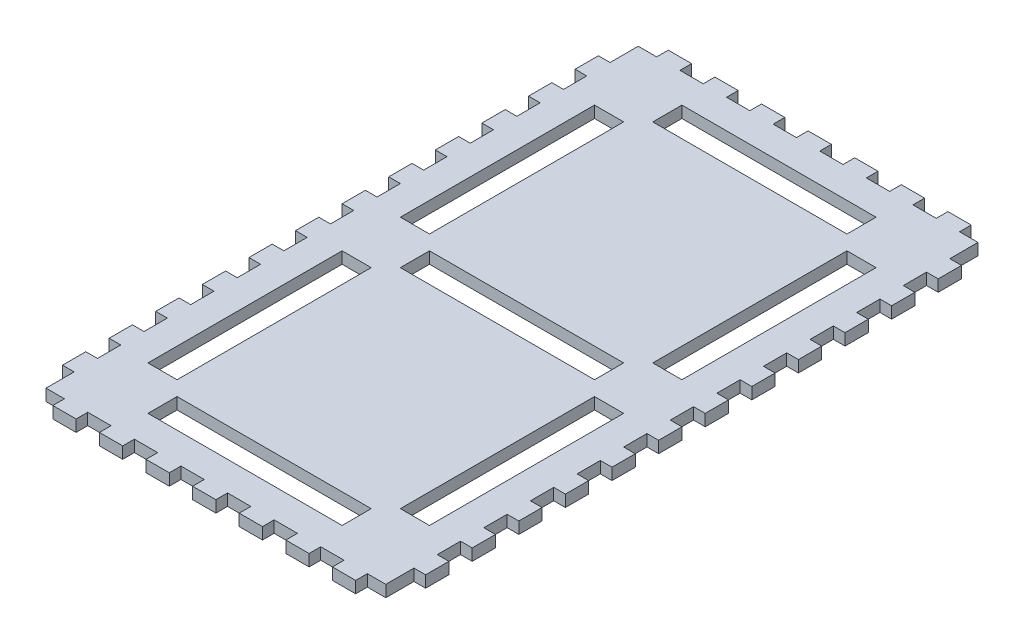
SolidWorks part; units mm, degrees
ref_plane "Front Plane" through (0, 0, 0) normal (0, 0, 1) x (1, 0, 0)
ref_plane "Top Plane" through (0, 0, 0) normal (0, 1, 0) x (1, 0, 0)
ref_plane "Right Plane" through (0, 0, 0) normal (1, 0, 0) x (0, 0, -1)
sketch "Sketch3" plane through (0, 0, 0) normal (0, 1, 0) x (1, 0, 0)
  line L1 (-87.5, -152.5) -> (87.5, -152.5)
  line L2 (-87.5, -152.5) -> (-87.5, 152.5)
  line L3 (-87.5, 152.5) -> (87.5, 152.5)
  line L4 (87.5, -152.5) -> (87.5, 152.5)
  line L5 (-87.5, -152.5) -> (87.5, 152.5) construction
  line L6 (-87.5, 152.5) -> (87.5, -152.5) construction
  line L7 (-50, 137.5) -> (50, 137.5)
  line L8 (-50, 137.5) -> (-50, 122.5)
  line L9 (-50, 122.5) -> (50, 122.5)
  line L10 (50, 137.5) -> (50, 122.5)
  line L22 (-72.5, 115) -> (-57.5, 115)
  line L23 (-72.5, 115) -> (-72.5, 15)
  line L24 (-72.5, 15) -> (-57.5, 15)
  line L25 (-57.5, 115) -> (-57.5, 15)
  line L26 (-50, -122.5) -> (50, -122.5)
  line L27 (-50, -122.5) -> (-50, -137.5)
  line L28 (-50, -137.5) -> (50, -137.5)
  line L29 (50, -122.5) -> (50, -137.5)
  line L34 (-50, 7.5) -> (50, 7.5)
  line L35 (-50, 7.5) -> (-50, -7.5)
  line L36 (-50, -7.5) -> (50, -7.5)
  line L37 (50, 7.5) -> (50, -7.5)
  line L42 (57.5, 115) -> (72.5, 115)
  line L43 (57.5, 115) -> (57.5, 15)
  line L44 (57.5, 15) -> (72.5, 15)
  line L45 (72.5, 115) -> (72.5, 15)
  line L46 (57.5, -15) -> (72.5, -15)
  line L47 (57.5, -15) -> (57.5, -115)
  line L48 (57.5, -115) -> (72.5, -115)
  line L49 (72.5, -15) -> (72.5, -115)
  line L50 (-72.5, -15) -> (-57.5, -15)
  line L51 (-72.5, -15) -> (-72.5, -115)
  line L52 (-72.5, -115) -> (-57.5, -115)
  line L53 (-57.5, -15) -> (-57.5, -115)
  line L74 (-54, 152.5) -> (-54, 158.5)
  line L79 (-78, 152.5) -> (-66, 152.5)
  line L80 (-78, 152.5) -> (-78, 158.5)
  line L81 (-78, 158.5) -> (-66, 158.5)
  line L82 (-66, 152.5) -> (-66, 158.5)
  line L83 (-54, 152.5) -> (-42, 152.5)
  line L84 (-42, 152.5) -> (-42, 158.5)
  line L85 (-54, 158.5) -> (-42, 158.5)
  line L86 (-30, 152.5) -> (-30, 158.5)
  line L87 (-30, 152.5) -> (-18, 152.5)
  line L88 (-18, 152.5) -> (-18, 158.5)
  line L89 (-30, 158.5) -> (-18, 158.5)
  line L90 (-6, 152.5) -> (-6, 158.5)
  line L91 (-6, 152.5) -> (6, 152.5)
  line L92 (6, 152.5) -> (6, 158.5)
  line L93 (-6, 158.5) -> (6, 158.5)
  line L94 (18, 152.5) -> (18, 158.5)
  line L95 (18, 152.5) -> (30, 152.5)
  line L96 (30, 152.5) -> (30, 158.5)
  line L97 (18, 158.5) -> (30, 158.5)
  line L98 (42, 152.5) -> (42, 158.5)
  line L99 (42, 152.5) -> (54, 152.5)
  line L100 (54, 152.5) -> (54, 158.5)
  line L101 (42, 158.5) -> (54, 158.5)
  line L102 (66, 152.5) -> (66, 158.5)
  line L103 (66, 152.5) -> (78, 152.5)
  line L104 (78, 152.5) -> (78, 158.5)
  line L105 (66, 158.5) -> (78, 158.5)
  line L106 (-87.5, 114) -> (-87.5, 102)
  line L107 (-87.5, 138) -> (-93.5, 138)
  line L108 (-87.5, 138) -> (-87.5, 126)
  line L109 (-87.5, 126) -> (-93.5, 126)
  line L110 (-93.5, 138) -> (-93.5, 126)
  line L111 (-87.5, 114) -> (-93.5, 114)
  line L112 (-93.5, 114) -> (-93.5, 102)
  line L113 (-87.5, 102) -> (-93.5, 102)
  line L114 (-87.5, 90) -> (-87.5, 78)
  line L115 (-87.5, 90) -> (-93.5, 90)
  line L116 (-93.5, 90) -> (-93.5, 78)
  line L117 (-87.5, 78) -> (-93.5, 78)
  line L118 (-87.5, 66) -> (-87.5, 54)
  line L119 (-87.5, 66) -> (-93.5, 66)
  line L120 (-93.5, 66) -> (-93.5, 54)
  line L121 (-87.5, 54) -> (-93.5, 54)
  line L122 (-87.5, 42) -> (-87.5, 30)
  line L123 (-87.5, 42) -> (-93.5, 42)
  line L124 (-93.5, 42) -> (-93.5, 30)
  line L125 (-87.5, 30) -> (-93.5, 30)
  line L126 (-87.5, 18) -> (-87.5, 6)
  line L127 (-87.5, 18) -> (-93.5, 18)
  line L128 (-93.5, 18) -> (-93.5, 6)
  line L129 (-87.5, 6) -> (-93.5, 6)
  line L130 (-87.5, -6) -> (-87.5, -18)
  line L131 (-87.5, -6) -> (-93.5, -6)
  line L132 (-93.5, -6) -> (-93.5, -18)
  line L133 (-87.5, -18) -> (-93.5, -18)
  line L134 (-87.5, -30) -> (-87.5, -42)
  line L135 (-87.5, -30) -> (-93.5, -30)
  line L136 (-93.5, -30) -> (-93.5, -42)
  line L137 (-87.5, -42) -> (-93.5, -42)
  line L138 (-87.5, -54) -> (-87.5, -66)
  line L139 (-87.5, -54) -> (-93.5, -54)
  line L140 (-93.5, -54) -> (-93.5, -66)
  line L141 (-87.5, -66) -> (-93.5, -66)
  line L142 (-87.5, -78) -> (-87.5, -90)
  line L143 (-87.5, -78) -> (-93.5, -78)
  line L144 (-93.5, -78) -> (-93.5, -90)
  line L145 (-87.5, -90) -> (-93.5, -90)
  line L146 (-87.5, -102) -> (-87.5, -114)
  line L147 (-87.5, -102) -> (-93.5, -102)
  line L148 (-93.5, -102) -> (-93.5, -114)
  line L149 (-87.5, -114) -> (-93.5, -114)
  line L150 (-87.5, -126) -> (-87.5, -138)
  line L151 (-87.5, -126) -> (-93.5, -126)
  line L152 (-93.5, -126) -> (-93.5, -138)
  line L153 (-87.5, -138) -> (-93.5, -138)
  line L154 (93.5, 114) -> (93.5, 102)
  line L155 (93.5, 102) -> (87.5, 102)
  line L156 (87.5, 114) -> (87.5, 102)
  line L157 (93.5, 114) -> (87.5, 114)
  line L158 (93.5, 138) -> (93.5, 126)
  line L159 (93.5, 138) -> (87.5, 138)
  line L160 (87.5, 138) -> (87.5, 126)
  line L161 (93.5, 126) -> (87.5, 126)
  line L162 (93.5, 90) -> (93.5, 78)
  line L163 (93.5, 78) -> (87.5, 78)
  line L164 (87.5, 90) -> (87.5, 78)
  line L165 (93.5, 90) -> (87.5, 90)
  line L166 (93.5, 66) -> (93.5, 54)
  line L167 (93.5, 54) -> (87.5, 54)
  line L168 (87.5, 66) -> (87.5, 54)
  line L169 (93.5, 66) -> (87.5, 66)
  line L170 (93.5, 42) -> (93.5, 30)
  line L171 (93.5, 30) -> (87.5, 30)
  line L172 (87.5, 42) -> (87.5, 30)
  line L173 (93.5, 42) -> (87.5, 42)
  line L174 (93.5, 18) -> (93.5, 6)
  line L175 (93.5, 6) -> (87.5, 6)
  line L176 (87.5, 18) -> (87.5, 6)
  line L177 (93.5, 18) -> (87.5, 18)
  line L178 (93.5, -6) -> (93.5, -18)
  line L179 (93.5, -18) -> (87.5, -18)
  line L180 (87.5, -6) -> (87.5, -18)
  line L181 (93.5, -6) -> (87.5, -6)
  line L182 (93.5, -30) -> (93.5, -42)
  line L183 (93.5, -42) -> (87.5, -42)
  line L184 (87.5, -30) -> (87.5, -42)
  line L185 (93.5, -30) -> (87.5, -30)
  line L186 (93.5, -54) -> (93.5, -66)
  line L187 (93.5, -66) -> (87.5, -66)
  line L188 (87.5, -54) -> (87.5, -66)
  line L189 (93.5, -54) -> (87.5, -54)
  line L190 (93.5, -78) -> (93.5, -90)
  line L191 (93.5, -90) -> (87.5, -90)
  line L192 (87.5, -78) -> (87.5, -90)
  line L193 (93.5, -78) -> (87.5, -78)
  line L194 (93.5, -102) -> (93.5, -114)
  line L195 (93.5, -114) -> (87.5, -114)
  line L196 (87.5, -102) -> (87.5, -114)
  line L197 (93.5, -102) -> (87.5, -102)
  line L198 (93.5, -126) -> (93.5, -138)
  line L199 (93.5, -138) -> (87.5, -138)
  line L200 (87.5, -126) -> (87.5, -138)
  line L201 (93.5, -126) -> (87.5, -126)
  line L202 (-87.5, 114) -> (93.5, 114) construction
  line L203 (66, -158.5) -> (66, -152.5)
  line L204 (66, -152.5) -> (78, -152.5)
  line L205 (78, -158.5) -> (78, -152.5)
  line L206 (66, -158.5) -> (78, -158.5)
  line L207 (42, -158.5) -> (42, -152.5)
  line L208 (42, -152.5) -> (54, -152.5)
  line L209 (54, -158.5) -> (54, -152.5)
  line L210 (42, -158.5) -> (54, -158.5)
  line L211 (18, -158.5) -> (18, -152.5)
  line L212 (18, -152.5) -> (30, -152.5)
  line L213 (30, -158.5) -> (30, -152.5)
  line L214 (18, -158.5) -> (30, -158.5)
  line L215 (-6, -158.5) -> (-6, -152.5)
  line L216 (-6, -152.5) -> (6, -152.5)
  line L217 (6, -158.5) -> (6, -152.5)
  line L218 (-6, -158.5) -> (6, -158.5)
  line L219 (-30, -158.5) -> (-30, -152.5)
  line L220 (-30, -152.5) -> (-18, -152.5)
  line L221 (-18, -158.5) -> (-18, -152.5)
  line L222 (-30, -158.5) -> (-18, -158.5)
  line L223 (-54, -158.5) -> (-54, -152.5)
  line L224 (-54, -152.5) -> (-42, -152.5)
  line L225 (-42, -158.5) -> (-42, -152.5)
  line L226 (-54, -158.5) -> (-42, -158.5)
  line L227 (-78, -158.5) -> (-78, -152.5)
  line L228 (-78, -158.5) -> (-66, -158.5)
  line L229 (-66, -158.5) -> (-66, -152.5)
  line L230 (-78, -152.5) -> (-66, -152.5)
  line L231 (66, 152.5) -> (66, -158.5) construction
  point P0 (0, 0)
  dimension "D14" = 12
  dimension "D15" = 6
  dimension "D2" = 15
  dimension "D3" = 100
  dimension "D4" = 15
  dimension "D5" = 30
  dimension "D6" = 7.5
  dimension "D7" = 115
  dimension "D8" = 7.5
  dimension "D9" = 7.5
  dimension "D10" = 7.5
  dimension "D11" = 15
  dimension "D12" = 15
  dimension "D13" = 15
  dimension "D16" = 7
  dimension "D17" = 9.5
  dimension "D18" = 12
  dimension "D19" = 12
  dimension "D20" = 6
  dimension "D22" = 14.5
  dimension "D23" = 12
  dimension "D24" = 2
  dimension "D25" = 181
  dimension "D27" = 311
  dimension "D21" = 12
  dimension "D26" = 2
extrude "Boss-Extrude4" add sketch "Sketch3" along normal blind 6 contours L219 L222 L221 L1 | L198 L201 L4 L199 | L182 L185 L4 L183 | L170 L173 L4 L171 | L105 L102 L3 L104 | L101 L98 L3 L100 | L97 L94 L3 L96 | L93 L90 L3 L92 | L89 L86 L3 L88 | L85 L74 L3 L84 | L3 L82 L81 L80 | L107 L110 L109 L2 | L113 L2 L111 L112 | L117 L2 L115 L116 | L129 L2 L127 L128 | L137 L2 L135 L136 | L141 L2 L139 L140 | L145 L2 L143 L144 | L149 L2 L147 L148 | L153 L2 L151 L152 | L25 L22 L23 L24 | L10 L7 L8 L9 | L45 L42 L43 L44 | L53 L50 L51 L52 | L228 L229 L230 L227 | L226 L225 L224 L223 | L214 L213 L212 L211 | L218 L217 L216 L215 | L210 L209 L208 L207 | L206 L205 L204 L203 | L194 L195 L196 L197 | L190 L191 L192 L193 | L186 L187 L188 L189 | L178 L179 L180 L181 | L166 L167 L168 L169 | L162 L163 L164 L165 | L154 L155 L156 L157 | L158 L161 L160 L159 | L120 L121 L118 L119 | L124 L125 L122 L123 | L132 L133 L130 L131 | L174 L175 L176 L177 | L49 L48 L47 L46 | L37 L36 L35 L34 | L29 L28 L27 L26
